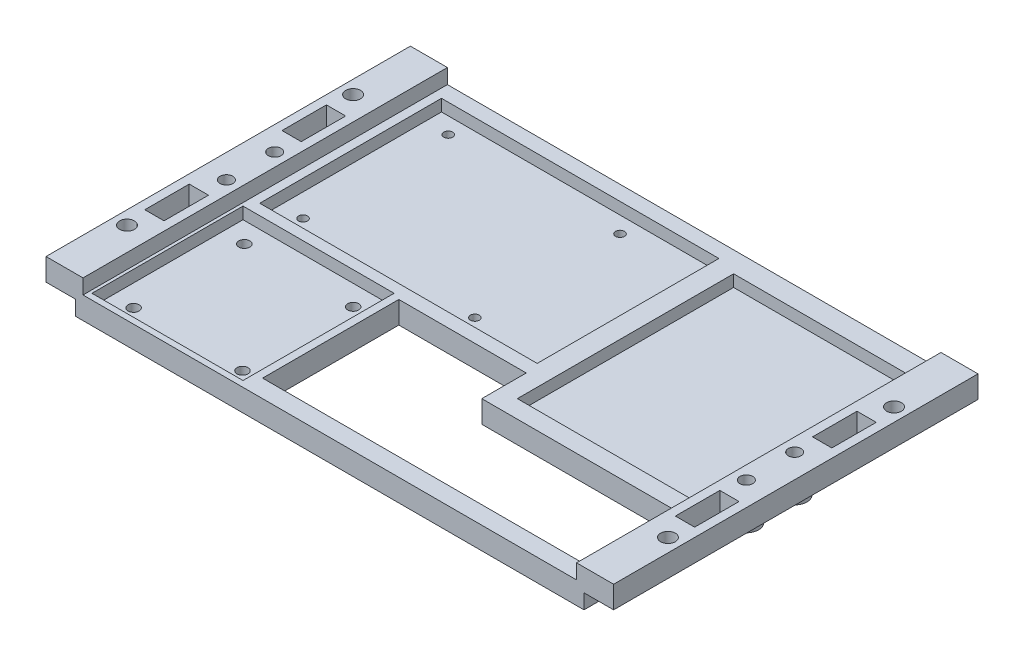
SolidWorks part; units mm, degrees
material "PET"
ref_plane "Front Plane" through (0, 0, 0) normal (0, 0, 1) x (1, 0, 0)
ref_plane "Top Plane" through (0, 0, 0) normal (0, 1, 0) x (1, 0, 0)
ref_plane "Right Plane" through (0, 0, 0) normal (1, 0, 0) x (0, 0, -1)
sketch "Sketch2" plane through (0, 0, 0) normal (0, 0, 1) x (1, 0, 0)
  line L0 (179.1, 12.5) -> (191.6, 12.5)
  line L1 (7.5, 0) -> (184.1, 0)
  line L2 (0, 5) -> (0, 12.5)
  line L3 (0, 12.5) -> (12.5, 12.5)
  line L4 (191.6, 5) -> (191.6, 12.5)
  line L7 (0, 5) -> (7.5, 5)
  line L8 (7.5, 0) -> (7.5, 5)
  line L11 (191.6, 5) -> (184.1, 5)
  line L12 (184.1, 0) -> (184.1, 5)
  line L14 (12.5, 12.5) -> (12.5, 7.5)
  line L15 (12.5, 7.5) -> (179.1, 7.5)
  line L16 (179.1, 12.5) -> (179.1, 7.5)
  dimension "D1" = 191.6
  dimension "D2" = 5
  dimension "D3" = 5
  dimension "D4" = 5
  dimension "D5" = 12.5
  dimension "D6" = 7.5
  dimension "D7" = 7.5
  dimension "D8" = 12.5
  dimension "D9" = 12.5
extrude "PlateFrame" add sketch "Sketch2" along normal blind 150
sketch "Sketch3" plane through (0, 12.5, 0) normal (0, 1, 0) x (1, 0, 0)
  line L0 (12.5, 0) -> (0, 0) construction
  line L2 (0, -150) -> (0, 0) construction
  line L3 (191.6, -150) -> (191.6, 0) construction
  line L4 (191.6, 0) -> (179.1, 0) construction
  circle A0 centre (8.05, -66.85) radius 2.5
  circle A1 centre (8.05, -83.15) radius 2.5
  circle A2 centre (183.55, -66.85) radius 2.5
  circle A3 centre (183.55, -83.15) radius 2.5
  dimension "D1" = 5
  dimension "D2" = 5
  dimension "D3" = 5
  dimension "D4" = 5
  dimension "D5" = 66.85
  dimension "D6" = 16.3
  dimension "D7" = 8.05
  dimension "D8" = 8.05
  dimension "D9" = 8.05
  dimension "D10" = 8.05
  dimension "D11" = 66.85
  dimension "D12" = 16.3
  dimension "D13" = 175.5
extrude "HoleSupport" cut sketch "Sketch3" against normal through all
sketch "Sketch4" plane through (0, 12.5, 0) normal (0, 1, 0) x (1, 0, 0)
  circle A0 centre (8.05, -66.85) radius 2.15
  circle A1 centre (8.05, -83.15) radius 2.15
  circle A2 centre (183.55, -83.15) radius 2.15
  circle A3 centre (183.55, -66.85) radius 2.15
  circle A4 centre (183.55, -66.85) radius 4.15
  circle A5 centre (183.55, -83.15) radius 4.15
  circle A6 centre (8.05, -66.85) radius 4.15
  circle A7 centre (8.05, -83.15) radius 4.15
  dimension "D1" = 2
extrude "CylindricalSupports" add sketch "Sketch4" against normal blind 12.5
sketch "Sketch5" plane through (0, 7.5, 0) normal (0, 1, 0) x (1, 0, 0)
  line L0 (12.5, -150) -> (12.5, 0) construction
  line L1 (17.5, -87) -> (60.5, -87)
  line L2 (12.5, -150) -> (12.5, 0) construction
  line L3 (17.5, -20) -> (107.15, -20)
  line L4 (17.5, -20) -> (17.5, -77.35)
  line L5 (17.5, -77.35) -> (107.15, -77.35)
  line L6 (107.15, -20) -> (107.15, -77.35)
  line L7 (174.1, -20) -> (116.1, -20)
  line L8 (174.1, -20) -> (174.1, -93)
  line L9 (174.1, -93) -> (116.1, -93)
  line L10 (116.1, -20) -> (116.1, -93)
  line L15 (179.1, -150) -> (179.1, 0) construction
  line L16 (179.1, 0) -> (12.5, 0) construction
  line L17 (17.5, -87) -> (17.5, -130)
  line L18 (17.5, -130) -> (60.5, -130)
  line L19 (60.5, -87) -> (60.5, -130)
  line L20 (179.1, -150) -> (12.5, -150) construction
  dimension "D1" = 5
  dimension "D2" = 89.65
  dimension "D3" = 57.35
  dimension "D4" = 5
  dimension "D5" = 43
  dimension "D6" = 58
  dimension "D7" = 43
  dimension "D8" = 20
  dimension "D9" = 20
  dimension "D10" = 5
  dimension "D11" = 73
  dimension "D12" = 20
extrude "ItemLayout" cut sketch "Sketch5" against normal blind 4
sketch "Sketch6" plane through (0, 7.5, 0) normal (0, 1, 0) x (1, 0, 0)
  line L1 (67.1, -84) -> (110.1, -84)
  line L2 (67.1, -84) -> (67.1, -130)
  line L3 (67.1, -130) -> (110.1, -130)
  line L4 (110.1, -84) -> (110.1, -99)
  line L9 (179.1, -150) -> (179.1, 0) construction
  line L10 (110.1, -130) -> (174.1, -130)
  line L12 (110.1, -99) -> (174.1, -99)
  line L13 (174.1, -130) -> (174.1, -99)
  line L14 (116.1, -93) -> (174.1, -93) construction
  line L15 (116.1, -20) -> (116.1, -93) construction
  line L17 (179.1, -150) -> (12.5, -150) construction
  dimension "D1" = 20
  dimension "D2" = 43
  dimension "D3" = 5
  dimension "D4" = 6
  dimension "D5" = 6
  dimension "D6" = 15
extrude "HoleCutout" cut sketch "Sketch6" against normal blind 7.5
sketch "Sketch7" plane through (0, 3.5, 0) normal (0, 1, 0) x (1, 0, 0)
  line L0 (17.5, -20) -> (17.5, -77.35) construction
  line L1 (17.5, -20) -> (17.5, -77.35) construction
  line L2 (107.15, -20) -> (17.5, -20) construction
  line L3 (107.15, -20) -> (17.5, -20) construction
  circle A0 centre (23.26, -23.5) radius 1.5
  circle A1 centre (23.26, -72.5) radius 1.5
  circle A2 centre (81.26, -72.5) radius 1.5
  circle A3 centre (81.26, -23.5) radius 1.5
  dimension "D1" = 3
  dimension "D2" = 3
  dimension "D3" = 3
  dimension "D4" = 3
  dimension "D5" = 5.76
  dimension "D6" = 5.76
  dimension "D7" = 3.5
  dimension "D8" = 3.5
  dimension "D9" = 58
  dimension "D10" = 58
  dimension "D11" = 49
  dimension "D12" = 49
extrude "HoleRaspberryPi" cut sketch "Sketch7" against normal blind 3.5
sketch "Sketch8" plane through (0, 3.5, 0) normal (0, 1, 0) x (1, 0, 0)
  line L0 (17.5, -130) -> (60.5, -130) construction
  line L1 (60.5, -87) -> (17.5, -87) construction
  line L2 (60.5, -130) -> (60.5, -87) construction
  line L3 (60.5, -130) -> (60.5, -87) construction
  line L4 (17.5, -87) -> (17.5, -130) construction
  line L5 (17.5, -130) -> (60.5, -130) construction
  circle A0 centre (57.56, -127.24) radius 1.85
  circle A1 centre (57.56, -89.86) radius 1.85
  circle A2 centre (20.81, -89.86) radius 1.85
  circle A3 centre (20.81, -127.24) radius 1.85
  dimension "D1" = 3.7
  dimension "D2" = 3.7
  dimension "D3" = 3.7
  dimension "D4" = 3.7
  dimension "D6" = 2.86
  dimension "D8" = 2.94
  dimension "D9" = 2.86
  dimension "D10" = 3.31
  dimension "D11" = 2.76
  dimension "D12" = 3.31
  dimension "D5" = 2.76
  dimension "D7" = 2.94
extrude "HoleMotorDriver" cut sketch "Sketch8" against normal blind 3.5
sketch "Sketch10" plane through (0, 7.5, 0) normal (0, 1, 0) x (1, 0, 0)
  line L1 (17.5, -87) -> (60.5, -87)
  line L2 (17.5, -87) -> (17.5, -130)
  line L3 (17.5, -130) -> (60.5, -130)
  line L4 (60.5, -87) -> (60.5, -130)
  line L5 (16.5, -86) -> (61.5, -86)
  line L6 (16.5, -86) -> (16.5, -131)
  line L7 (16.5, -131) -> (61.5, -131)
  line L8 (61.5, -86) -> (61.5, -131)
  dimension "D1" = 1
  dimension "D2" = 1
  dimension "D3" = 1
  dimension "D4" = 1
extrude "CutMotorDriver" cut sketch "Sketch10" against normal blind 4
sketch "Sketch11" plane through (0, 7.5, 0) normal (0, 1, 0) x (1, 0, 0)
  line L1 (17.5, -20) -> (107.15, -20)
  line L2 (17.5, -20) -> (17.5, -77.35)
  line L3 (17.5, -77.35) -> (107.15, -77.35)
  line L4 (107.15, -20) -> (107.15, -77.35)
  line L5 (109.15, -79.35) -> (15.5, -79.35)
  line L6 (109.15, -79.35) -> (109.15, -18)
  line L7 (109.15, -18) -> (15.5, -18)
  line L8 (15.5, -79.35) -> (15.5, -18)
  dimension "D1" = 2
  dimension "D2" = 2
  dimension "D3" = 2
  dimension "D4" = 2
extrude "CutPaspberryPi" cut sketch "Sketch11" against normal blind 4
sketch "Sketch12" plane through (0, 12.5, 0) normal (0, 1, 0) x (1, 0, 0)
  line L0 (191.6, -150) -> (191.6, 0) construction
  line L1 (0, 0) -> (191.6, 0)
  line L2 (0, 0) -> (0, -13)
  line L3 (0, -13) -> (191.6, -13)
  line L4 (191.6, 0) -> (191.6, -13)
  line L6 (0, -150) -> (191.6, -150)
  line L7 (0, -150) -> (0, -136)
  line L8 (0, -136) -> (191.6, -136)
  line L9 (191.6, -150) -> (191.6, -136)
  dimension "D1" = 13
  dimension "D2" = 14
extrude "CutPlateEdges" cut sketch "Sketch12" against normal blind 12.5
sketch "Sketch13" plane through (0, 12.5, 0) normal (0, 1, 0) x (1, 0, 0)
  line L0 (12.5, -136) -> (12.5, -13) construction
  line L1 (9.5, -59.35) -> (3, -59.35)
  line L2 (9.5, -59.35) -> (9.5, -44.35)
  line L3 (9.5, -44.35) -> (3, -44.35)
  line L4 (3, -59.35) -> (3, -44.35)
  line L5 (3, -90.65) -> (9.5, -90.65)
  line L6 (3, -90.65) -> (3, -105.65)
  line L7 (3, -105.65) -> (9.5, -105.65)
  line L8 (9.5, -90.65) -> (9.5, -105.65)
  line L9 (182.1, -59.35) -> (188.6, -59.35)
  line L10 (182.1, -59.35) -> (182.1, -44.35)
  line L11 (182.1, -44.35) -> (188.6, -44.35)
  line L12 (188.6, -59.35) -> (188.6, -44.35)
  line L13 (182.1, -90.65) -> (188.6, -90.65)
  line L14 (182.1, -90.65) -> (182.1, -105.65)
  line L15 (182.1, -105.65) -> (188.6, -105.65)
  line L16 (188.6, -90.65) -> (188.6, -105.65)
  line L18 (179.1, -136) -> (179.1, -13) construction
  line L19 (179.1, -136) -> (179.1, -13) construction
  circle A4 centre (8.05, -66.85) radius 2.15 construction
  circle A5 centre (8.05, -83.15) radius 2.15 construction
  circle A6 centre (183.55, -66.85) radius 2.15 construction
  circle A7 centre (183.55, -83.15) radius 2.15 construction
  dimension "D2" = 7.5
  dimension "D9" = 7.5
  dimension "D10" = 7.5
  dimension "D3" = 3
  dimension "D4" = 6.5
  dimension "D5" = 15
  dimension "D6" = 3
  dimension "D7" = 6.5
  dimension "D8" = 15
  dimension "D11" = 3
  dimension "D12" = 3
  dimension "D13" = 6.5
  dimension "D14" = 6.5
  dimension "D15" = 15
  dimension "D16" = 15
  dimension "D17" = 7.5
extrude "CutShellHoles" cut sketch "Sketch13" against normal blind 12.5
sketch "Sketch14" plane through (0, 7.5, 0) normal (0, 1, 0) x (1, 0, 0)
  line L0 (61.5, -131) -> (61.5, -86) construction
  line L1 (64.5, -83) -> (13.5, -83)
  line L2 (64.5, -83) -> (64.5, -134)
  line L3 (64.5, -134) -> (13.5, -134)
  line L4 (13.5, -83) -> (13.5, -134)
  line L5 (16.5, -86) -> (16.5, -131) construction
  line L6 (16.5, -131) -> (61.5, -131) construction
  line L7 (61.5, -86) -> (16.5, -86) construction
  dimension "D1" = 3
  dimension "D2" = 3
  dimension "D3" = 3
  dimension "D4" = 3
extrude "CutMotorDriver2" cut sketch "Sketch14" against normal blind 4
sketch "Sketch15" plane through (0, 12.5, 0) normal (0, 1, 0) x (1, 0, 0)
  line L0 (12.5, -136) -> (12.5, -13) construction
  line L1 (12.5, -136) -> (12.5, -13) construction
  line L2 (179.1, -136) -> (179.1, -13) construction
  line L3 (179.1, -136) -> (179.1, -13) construction
  circle A0 centre (4.5, -36.85) radius 2.5
  circle A1 centre (4.5, -113.15) radius 2.5
  circle A2 centre (187.1, -113.15) radius 2.5
  circle A3 centre (187.1, -36.85) radius 2.5
  circle A4 centre (8.05, -66.85) radius 2.15 construction
  circle A5 centre (8.05, -83.15) radius 2.15 construction
  circle A6 centre (183.55, -66.85) radius 2.15 construction
  circle A7 centre (183.55, -83.15) radius 2.15 construction
  dimension "D2" = 30
  dimension "D3" = 5
  dimension "D4" = 8
  dimension "D5" = 8
  dimension "D6" = 5
  dimension "D7" = 30
  dimension "D8" = 30
  dimension "D9" = 5
  dimension "D10" = 5
  dimension "D11" = 8
  dimension "D1" = 30
  dimension "D12" = 8
extrude "StandoffHoles" cut sketch "Sketch15" against normal through all
sketch "Sketch16" plane through (0, 0, 0) normal (0, -1, 0) x (1, 0, 0)
  line L1 (7.5, 136) -> (10, 136)
  line L2 (7.5, 136) -> (7.5, 108)
  line L3 (7.5, 108) -> (10, 108)
  line L4 (10, 136) -> (10, 108)
  line L5 (184.1, 136) -> (181.6, 136)
  line L6 (184.1, 136) -> (184.1, 108)
  line L7 (184.1, 108) -> (181.6, 108)
  line L8 (181.6, 136) -> (181.6, 108)
  line L9 (184.1, 13) -> (181.6, 13)
  line L10 (184.1, 13) -> (184.1, 41)
  line L11 (184.1, 41) -> (181.6, 41)
  line L12 (181.6, 13) -> (181.6, 41)
  line L13 (7.5, 13) -> (10, 13)
  line L14 (7.5, 13) -> (7.5, 41)
  line L15 (7.5, 41) -> (10, 41)
  line L16 (10, 13) -> (10, 41)
  dimension "D1" = 28
  dimension "D2" = 2.5
  dimension "D3" = 28
  dimension "D4" = 28
  dimension "D5" = 28
  dimension "D6" = 2.5
  dimension "D7" = 2.5
  dimension "D8" = 2.5
extrude "Cut-Extrude1" cut sketch "Sketch16" against normal blind 5
